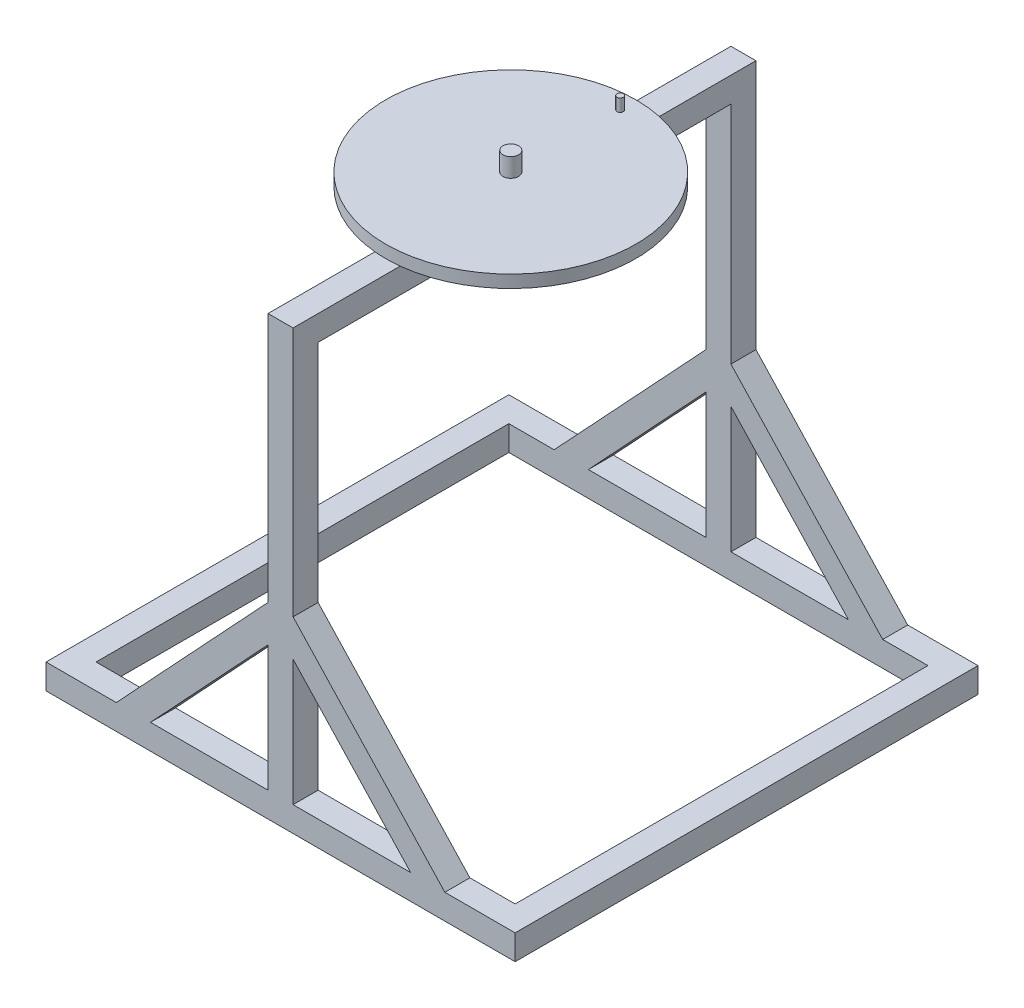
SolidWorks part; units mm, degrees
ref_plane "Front Plane" through (0, 0, 0) normal (0, 0, 1) x (1, 0, 0)
ref_plane "Top Plane" through (0, 0, 0) normal (0, 1, 0) x (1, 0, 0)
ref_plane "Right Plane" through (0, 0, 0) normal (1, 0, 0) x (0, 0, -1)
sketch "Sketch1" plane through (0, 0, 0) normal (0, 0, 1) x (1, 0, 0)
  line L2 (-79.4702, 173.5099) -> (-79.4702, -226.4901)
  line L6 (-459.4702, -526.4901) -> (340.5298, -526.4901)
  line L7 (-79.4702, -285.1137) -> (-79.4702, -486.4901)
  line L10 (-59.4702, 503.1381) -> (-59.4702, 173.5099) construction
  line L12 (-79.4702, 173.5099) -> (-39.4702, 173.5099)
  line L13 (-322.1369, -486.4901) -> (-79.4702, -226.4901)
  line L14 (340.5298, -486.4901) -> (340.5298, -526.4901)
  line L15 (-79.4702, -486.4901) -> (-267.4214, -486.4901)
  line L16 (-267.4214, -486.4901) -> (-79.4702, -285.1137)
  line L17 (-79.4702, -285.1137) -> (-79.4702, -486.4901)
  line L18 (-267.4214, -486.4901) -> (-79.4702, -486.4901)
  line L19 (-459.4702, -486.4901) -> (-322.1369, -486.4901)
  line L20 (-459.4702, -486.4901) -> (-459.4702, -526.4901)
  line L22 (340.5298, -486.4901) -> (203.1965, -486.4901)
  line L23 (148.481, -486.4901) -> (-39.4702, -486.4901)
  line L24 (-39.4702, -285.1137) -> (-39.4702, -486.4901)
  line L25 (148.481, -486.4901) -> (-39.4702, -285.1137)
  line L26 (-39.4702, -486.4901) -> (148.481, -486.4901)
  line L27 (203.1965, -486.4901) -> (-39.4702, -226.4901)
  line L28 (-39.4702, -285.1137) -> (-39.4702, -486.4901)
  line L29 (-39.4702, 173.5099) -> (-39.4702, -226.4901)
  line L30 (-59.4702, -526.4901) -> (-59.4702, -1036.4248) construction
  point P6 (-59.4702, -526.4901)
  point P17 (-59.4702, 173.5099)
  dimension "D1" = 40
  dimension "D4" = 20
extrude "Boss-Extrude1" add sketch "Sketch1" along normal blind 740
sketch "Sketch2" plane through (0, -526.4901, 0) normal (0, -1, 0) x (1, 0, 0)
  line L0 (-459.4702, 740) -> (340.5298, 740) construction
  line L1 (-419.4702, 700) -> (300.5298, 700)
  line L2 (-419.4702, 700) -> (-419.4702, 40)
  line L3 (-419.4702, 40) -> (300.5298, 40)
  line L4 (300.5298, 700) -> (300.5298, 40)
  line L5 (-459.4702, 740) -> (-459.4702, 0) construction
  line L6 (-459.4702, 0) -> (340.5298, 0) construction
  line L7 (340.5298, 740) -> (340.5298, 0) construction
  dimension "D1" = 40
  dimension "D2" = 40
  dimension "D3" = 40
  dimension "D4" = 40
extrude "Cut-Extrude1" cut sketch "Sketch2" against normal blind 760
sketch "Sketch3" plane through (0, 273.5099, 0) normal (0, 1, 0) x (1, 0, 0)
  line L1 (-79.4702, 0) -> (-39.4702, 0) construction
  circle A0 centre (-59.4702, -400) radius 201.4701
  point P6 (-59.4702, 0)
  dimension "D1" = 402.9401
sketch "Sketch4" plane through (0, 0, 0) normal (0, 0, -1) x (-1, 0, 0)
  line L0 (459.4702, -526.4901) -> (-340.5298, -526.4901) construction
  line L1 (59.4702, -526.4901) -> (-315.5298, -526.4901)
  line L3 (59.4702, -486.4901) -> (-315.5298, -486.4901)
  line L4 (-315.5298, -526.4901) -> (-315.5298, -486.4901)
  line L5 (-340.5298, -486.4901) -> (-203.1965, -486.4901) construction
  line L7 (59.4702, -486.4901) -> (434.4702, -486.4901)
  line L9 (59.4702, -526.4901) -> (434.4702, -526.4901)
  line L10 (434.4702, -486.4901) -> (434.4702, -526.4901)
  line L11 (-340.5298, -486.4901) -> (459.4702, -486.4901)
  line L12 (-340.5298, -486.4901) -> (-340.5298, -526.4901)
  line L13 (-340.5298, -526.4901) -> (459.4702, -526.4901)
  line L14 (459.4702, -486.4901) -> (459.4702, -526.4901)
  line M5 (-203.1965, -486.4901) -> (-340.5298, -486.4901)
  line M6 (-340.5298, -486.4901) -> (-340.5298, -526.4901)
  line M7 (-340.5298, -526.4901) -> (459.4702, -526.4901)
  line M8 (459.4702, -526.4901) -> (459.4702, -486.4901)
  line M9 (459.4702, -486.4901) -> (322.1369, -486.4901)
  dimension "D1" = 375
  dimension "D2" = 375
extrude "Cut-Extrude2" cut sketch "Sketch4" against normal blind 817 contours L4 M7 M5 M6 | L10 M9 M7 M8
sketch "Sketch5" plane through (0, 0, 0) normal (0, 0, -1) x (-1, 0, 0)
  line L0 (434.4702, -526.4901) -> (-315.5298, -526.4901) construction
  line L1 (-315.5298, -486.4901) -> (-275.5298, -486.4901)
  line L2 (-315.5298, -486.4901) -> (-315.5298, -526.4901)
  line L3 (-315.5298, -526.4901) -> (-275.5298, -526.4901)
  line L4 (-275.5298, -486.4901) -> (-275.5298, -526.4901)
  line L6 (434.4702, -486.4901) -> (394.4702, -486.4901)
  line L7 (434.4702, -486.4901) -> (434.4702, -526.4901)
  line L8 (434.4702, -526.4901) -> (394.4702, -526.4901)
  line L9 (394.4702, -486.4901) -> (394.4702, -526.4901)
  dimension "D1" = 40
  dimension "D2" = 40
extrude "Boss-Extrude2" add sketch "Sketch5" against normal blind 740
sketch "Sketch6" plane through (0, 0, 0) normal (0, 0, -1) x (-1, 0, 0)
  line L0 (79.4702, 173.5099) -> (79.4702, -226.4901) construction
  line L1 (39.4702, 173.5099) -> (79.4702, 173.5099)
  line L2 (39.4702, 173.5099) -> (39.4702, 133.5099)
  line L3 (39.4702, 133.5099) -> (79.4702, 133.5099)
  line L4 (79.4702, 173.5099) -> (79.4702, 133.5099)
  dimension "D1" = 40
extrude "Boss-Extrude3" add sketch "Sketch6" against normal blind 740
sketch "Sketch7" plane through (0, 173.5099, 0) normal (0, 1, 0) x (1, 0, 0)
  circle A0 centre (-61.4033, -370) radius 200
  dimension "D1" = 400
extrude "Boss-Extrude5" add sketch "Sketch7" along normal blind 20
sketch "Sketch8" plane through (0, 193.5099, 0) normal (0, 1, 0) x (1, 0, 0)
  circle A0 centre (-61.4033, -370) radius 12.5
  dimension "D1" = 25
extrude "Boss-Extrude6" add sketch "Sketch8" along normal blind 30
sketch "Sketch9" plane through (0, 193.5099, 0) normal (0, 1, 0) x (1, 0, 0)
  circle A0 centre (-59.8768, -196.6979) radius 5
  point P2 (-60.3535, -216.4824)
  dimension "D1" = 10
extrude "Boss-Extrude10" add sketch "Sketch9" along normal blind 20 contours A0
